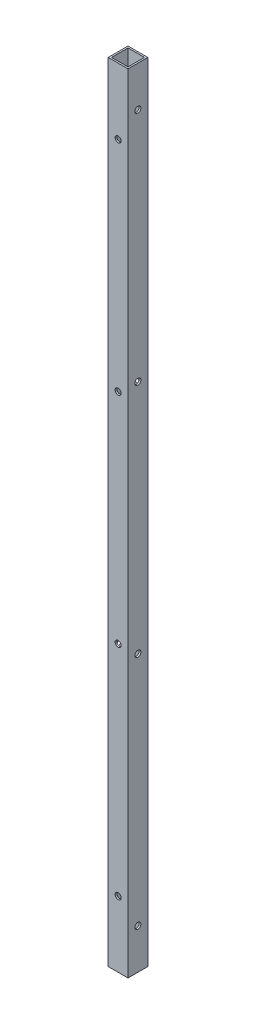
SolidWorks part; units mm, degrees
material "1060 Alloy"
ref_plane "Front Plane" through (0, 0, 0) normal (0, 0, 1) x (1, 0, 0)
ref_plane "Top Plane" through (0, 0, 0) normal (0, 1, 0) x (1, 0, 0)
ref_plane "Right Plane" through (0, 0, 0) normal (1, 0, 0) x (0, 0, -1)
sketch "Sketch1" plane through (0, 0, 0) normal (0, 1, 0) x (1, 0, 0)
  line L1 (-9.525, 9.525) -> (9.525, 9.525)
  line L2 (-9.525, 9.525) -> (-9.525, -9.525)
  line L3 (-9.525, -9.525) -> (9.525, -9.525)
  line L4 (9.525, 9.525) -> (9.525, -9.525)
  line L5 (-9.525, 9.525) -> (9.525, -9.525) construction
  line L6 (-9.525, -9.525) -> (9.525, 9.525) construction
  line L7 (-7.9375, 7.9375) -> (7.9375, 7.9375)
  line L8 (-7.9375, 7.9375) -> (-7.9375, -7.9375)
  line L9 (-7.9375, -7.9375) -> (7.9375, -7.9375)
  line L10 (7.9375, 7.9375) -> (7.9375, -7.9375)
  line L11 (-7.9375, 7.9375) -> (7.9375, -7.9375) construction
  line L12 (-7.9375, -7.9375) -> (7.9375, 7.9375) construction
  point P0 (0, 0)
  point P5 (0, 0)
  dimension "D2" = 19.05
  dimension "D1" = 19.05
  dimension "D3" = 15.875
  dimension "D4" = 15.875
extrude "Tube" add sketch "Sketch1" along normal blind 758.9266
sketch "Sketch2" plane through (0, 0, 9.525) normal (0, 0, 1) x (1, 0, 0)
  line L0 (0, 758.9266) -> (0, 777.9766) construction
  line L1 (0, 777.9766) -> (0, 781.05) construction
  line L6 (0, 695.325) -> (0, 758.9266) construction
  line L7 (-9.525, 758.9266) -> (9.525, 758.9266) construction
  circle A2 centre (0, 695.325) radius 2.8956
  dimension "D1" = 5.7912
  dimension "D2" = 19.05
  dimension "D3" = 3.0734
  dimension "D4" = 85.725
extrude "Side Wall Holes" cut sketch "Sketch2" against normal through all
pattern_linear "LPattern1" count 4 spacing 210.5745 along (0, -1, 0) of "Side Wall Holes"
sketch "Sketch3" plane through (-9.525, 0, 0) normal (-1, 0, 0) x (0, 0, 1)
  line L0 (0, 758.9266) -> (0, 720.09) construction
  line L1 (-9.525, 758.9266) -> (9.525, 758.9266) construction
  line L2 (0, 758.9266) -> (0, 777.9766) construction
  line L3 (0, 777.9766) -> (0, 781.05) construction
  circle A0 centre (0, 720.09) radius 2.8956
  dimension "D1" = 5.7912
  dimension "D2" = 3.0734
  dimension "D4" = 60.96
extrude "RearWallHoles" cut sketch "Sketch3" against normal through all
pattern_linear "LPattern2" count 4 spacing 227.0845 along (0, -1, 0) of "RearWallHoles"
equation "\"Height\"= 32in"
equation "\"Width\"= 23in"
equation "\"Depth\"= 20in"
equation "\"Plexi\"= .121in"
equation "\"Cutwidth\"= .016in"
equation "\"Earsize\"= 1in + \"Cutwidth\" /2"
equation "\"Slotsize\" = 1in - \"CutWidth\" / 2"
equation "\"InnerWidth\" = \"Width\" - 2* \"Plexi\""
equation "\"InnerHeight\" = \"Height\" -2 * \"Plexi\""
equation "\"RearHoleSpacing\" = (\"Width\" - 2*\"RearHolesBorder\") / (\"RearNumHoles\"-1)"
equation "\"RivetDia\" = .228in"
equation "\"SlotDepth\" = \"Plexi\" + 0.75in + .005in"
equation "\"SideSlotWidth\"   = \"Plexi\"+.005in"
equation "\"D1@Sketch2\"=\"RivetDia\""
equation "\"D2@Sketch2\"=\"CornerCube\""
equation "\"SidePanelVertSpacing\" = (\"Height\"-2*(1.75-\"Plexi\")) / 5"
equation "\"MagnetThickness\"= 0.125in"
equation "\"MagnetDiameter\"= 12mm"
equation "\"DoorPlexi\" = \"Plexi\""
equation "\"Boxsize\" = .75in"
equation "\"Boxinner\" = .625in"
equation "\"CornerCube\" = 0.75in"
equation "\"FingerLength\" = 1.125in"
equation "\"InnerDepth\" = \"Depth\" - 2*\"Plexi\""
equation "\"RearNumHoles\" = 4"
equation "\"RearHolesBorder\" = 2.25"
equation "\"RearBarLength\" = (\"InnerWidth\"-2*\"CornerCube\")"
equation "\"RearTopNumHoles\" = 4"
equation "\"RearTopHolesBorder\" = 3.1"
equation "\"RearTopHolesSpacing\" = (\"Width\" - 2*\"RearTopHolesBorder\") / (\"RearTopNumHoles\"-1)"
equation "\"SideTopNumHoles\" = 4"
equation "\"SideTopHoleOffset\"=\"CornerCube\"+\"FingerLength\"+\"Plexi\"+.5"
equation "\"SideTopHoleSpacing\" = (\"TopBarDepth\"-2*\"SideTopHoleOffset\") / (\"SideTopNumHoles\"-1)"
equation "\"SideHorizNumHoles\" = 4"
equation "\"SideHorizHoleBorder\" = 1.50"
equation "\"SideHorizHoleSpacing\" = (\"TopBarDepth\"-2*\"SideHorizHoleBorder\") / (\"SideHorizNumHoles\"-1)"
equation "\"SideVertNumHoles\" = 4"
equation "\"SideVertHolesBorder\" = \"CornerCube\"+\"FingerLength\"+1.50"
equation "\"SideVertHoleSpacing\" = (\"SideVertBarLength\" - 2*(\"SideVertHolesBorder\"-\"Plexi\"-\"CornerCube\")) / (\"SideVertNumHoles\"-1)"
equation "\"BottomPanelSideHoleSpacing\" = (\"InnerDepth\"-2*(1.75-\"Plexi\")) / 4"
equation "\"FrontDoorGap\" = .1in"
equation "\"TopDepth\" = \"Depth\"-\"DoorPlexi\"-\"FrontDoorGap\""
equation "\"TopBarDepth\" = \"Depth\"-\"DoorPlexi\"-\"Plexi\"-2*\"MagnetThickness\"-2*\"CornerCube\""
equation "\"D3@Sketch2\"=\"Plexi\""
equation "\"D4@Sketch2\"=\"SideVertHolesBorder\""
equation "\"D3@LPattern1\"=\"SideVertHoleSpacing\""
equation "\"D1@LPattern1\"=\"SideVertNumHoles\""
equation "\"BasePlateThickness\" = 0.5in"
equation "\"SideVertBarLength\"=\"Height\"-\"BasePlateThickness\"-2*\"CornerCube\"-\"Plexi\""
equation "\"RearSideVertNumHoles\" = 4"
equation "\"RearSideVertHolesBorder\" = 2.4"
equation "\"RearSideVertHoleSpacing\" = (\"SideVertBarLength\" - 2*(\"RearSideVertHolesBorder\"-\"Plexi\"-\"CornerCube\")) / (\"RearSideVertNumHoles\"-1)"
equation "\"D1@Tube\"=\"SideVertBarLength\""
equation "\"D1@Sketch3\"=\"RivetDia\""
equation "\"D2@Sketch3\"=\"Plexi\""
equation "\"D3@Sketch3\"=\"CornerCube\""
equation "\"D4@Sketch3\"=\"RearSideVertHolesBorder\""
equation "\"D3@LPattern2\"=\"RearSideVertHoleSpacing\""
equation "\"D1@LPattern2\"=\"RearSideVertNumHoles\""
equation "\"D3@Sketch1\"=\"Boxinner\""
equation "\"D4@Sketch1\"=\"Boxinner\""
equation "\"EBWidth\" = 9in"
equation "\"BasePlateWidth\" = \"Width\"+\"EBWidth\"-2*\"Plexi\""
equation "\"BasePlateDepth\" = \"TopBarDepth\"+2*\"CornerCube\""
equation "\"BoxsizeHalf\" = \"Boxsize\"/2"
equation "\"FingerWidth\" = .625in"
equation "\"CoolerDepth\" = 12in"
equation "\"ShelfGap\" = 0.5in"
equation "\"ShelfDepth\" = \"TopBarDepth\"+\"CornerCube\"-\"CoolerDepth\""
equation "\"ShelfBarDepth\"=\"ShelfDepth\"-2*\"CornerCube\""
equation "\"ShelfWidth\" = \"EBWidth\"-\"ShelfGap\""
equation "\"ShelfBarWidth\" = \"EBWidth\"-\"Boxsize\""
equation "\"ShelfBarWidthShort\" = \"ShelfBarWidth\"-\"Boxsize\"-\"ShelfGap\""
equation "\"IntakeWidth\"=4in"
equation "\"IntakeHeight\"=2in"
equation "\"ExhaustWidth\"=4in"
equation "\"ExhaustHeight\"=2in"
equation "\"VentSpacing\"=7in"
equation "\"AngleBracketLength\"=20mm"
equation "\"AngleBracketWidth\"=.5in"
equation "\"AngleBracketThickness\"=.125in"
equation "\"AngleBracketHolePos\"=15mm"
equation "\"AngleBracketHoleDia\"=\"Rivet3_16Dia\""
equation "\"ShelfBarAngleHole\"=\"ShelfGap\"+\"Boxsize\"+\"AngleBracketHolePosShort\""
equation "\"ComponentMountDia\"=0.1770"
equation "\"ShelfThickness\" = .1250in"
equation "\"Rivet3_16Dia\" = .191in"
equation "\"BinderPostDia\" = .228in"
equation "\"ShelfHeight1\" = 13in"
equation "\"ShelfHeight2\" = 24in"
equation "\"VentVertLocation\"=12.75in"
equation "\"AngleBracketLengthShort\"=.625in"
equation "\"AngleBracketLengthLong\"=1in"
equation "\"AngleBracketHolePosShort\"=.358in"
equation "\"AngleBracketHolePosLong\"=.7in"
equation "\"PSBracketThickness\" = .0641in"
equation "\"EBForwardMountOffset\" = 4.0in"
equation "\"EBForwardMount\" = 2*\"Boxsize\"+\"CoolerDepth\"+\"EBForwardMountOffset\""
equation "\"EBRearwardMountOffset\" = 1.5in"
equation "\"EBRearwardMount\"= \"Boxsize\"+\"EBRearwardMountOffset\""
equation "\"MagSealWidth\" = \"InnerWidth\""
equation "\"MagSealHeight\" = \"Height\"-\"BasePlateThickness\"-\"Plexi\""
equation "\"MagWidth\" = .500in"
equation "\"SiliconeSealOD\" = .3125in"
equation "\"SiliconeSealID\" = .1875in"
equation "\"SiliconeSealWidth\" = \"MagSealWidth\" - 2*\"MagWidth\"-\"SiliconeSealOD\""
equation "\"SiliconeSealHeigth\" = \"MagSealHeight\" - 2*\"MagWidth\"-\"SiliconeSealOD\""
equation "\"HooknLoopThick\" = .085in"
equation "\"HooknLoopWidth\" = 0.75in"
equation "\"HooknLoopHeigth\" = 0.75in"
equation "\"RivNutHeight\" = 0.015in"
